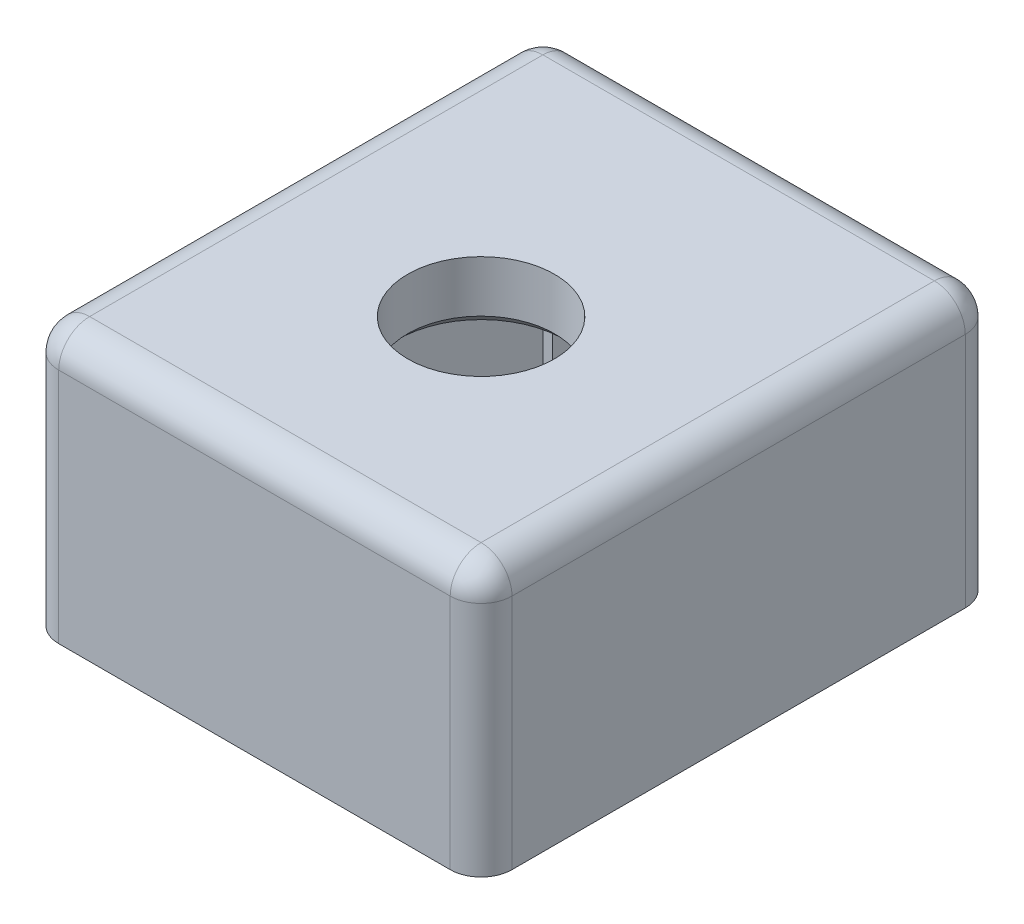
SolidWorks part; units mm, degrees
ref_plane "Front Plane" through (0, 0, 0) normal (0, 0, 1) x (1, 0, 0)
ref_plane "Top Plane" through (0, 0, 0) normal (0, 1, 0) x (1, 0, 0)
ref_plane "Right Plane" through (0, 0, 0) normal (1, 0, 0) x (0, 0, -1)
sketch "Sketch1" plane through (0, 0, 0) normal (0, 1, 0) x (1, 0, 0)
  line L0 (0, 0) -> (8.5, 0) construction
  line L1 (0, 0) -> (-11, 0) construction
  line L2 (8.5, -1.375) -> (6.5, -1.375) construction
  line L3 (8.5, -1.375) -> (8.5, 1.375) construction
  line L4 (8.5, 1.375) -> (6.5, 1.375) construction
  line L5 (6.5, -1.375) -> (6.5, 1.375) construction
  line L6 (8.5, -1.375) -> (6.5, 1.375) construction
  line L7 (8.5, 1.375) -> (6.5, -1.375) construction
  line L8 (11, -11) -> (-11, -11)
  line L9 (11, -11) -> (11, 14)
  line L10 (11, 14) -> (-11, 14)
  line L11 (-11, -11) -> (-11, 14)
  line L12 (11, -11) -> (-11, 14) construction
  line L13 (11, 14) -> (-11, -11) construction
  line L14 (0, 0) -> (0, -11) construction
  line L15 (0, 0) -> (0, 14) construction
  circle A0 centre (0, 0) radius 8.5 construction
  circle A1 centre (0, 0) radius 3.5625
  point P2 (0, 1.5)
  point P6 (7.5, 0)
  point P13 (8.5, 0)
  dimension "D1" = 17
  dimension "D2" = 7.125
  dimension "D3" = 2.75
  dimension "D4" = 2
  dimension "D5" = 25
  dimension "D6" = 22
extrude "Boss-Extrude1" add sketch "Sketch1" along normal blind 3
sketch3d "3DSketch1"
  line L0 (0, 0, 0) -> (8.5, 0, 0) construction
  line L1 (8.5, 0, -1.375) -> (6.5, 0, -1.375)
  line L2 (8.5, 0, -1.375) -> (8.5, 0, 1.375)
  line L3 (8.5, 0, 1.375) -> (6.5, 0, 1.375)
  line L4 (6.5, 0, -1.375) -> (6.5, 0, 1.375)
  line L5 (8.5, 0, -1.375) -> (6.5, 0, 1.375) construction
  line L6 (8.5, 0, 1.375) -> (6.5, 0, -1.375) construction
  point P0 (7.5, 0, 0)
  dimension "D1" = 8.5
  dimension "D2" = 2
  dimension "D3" = 2.75
extrude "Cut-Extrude1" cut sketch "3DSketch1" along direction (0, -1, 0) on the side against the normal blind 2
sketch "Sketch2" plane through (0, 0, 0) normal (0, -1, 0) x (1, 0, 0)
  line L0 (-11, 11) -> (11, 11) construction
  line L1 (11, -14) -> (-11, -14)
  line L2 (11, -14) -> (11, 11)
  line L3 (11, 11) -> (-11, 11)
  line L4 (-11, -14) -> (-11, 11)
  line L5 (11, -14) -> (-11, 11) construction
  line L6 (11, 11) -> (-11, -14) construction
  line L7 (-11, -14) -> (-11, 11) construction
  line L8 (9, 9) -> (-9, 9)
  line L9 (-9, -12) -> (-9, 9)
  line L10 (9, -12) -> (-9, -12)
  line L11 (9, -12) -> (9, 9)
  point P0 (0, -1.5)
  dimension "D1" = 2
extrude "Boss-Extrude2" add sketch "Sketch2" along normal blind 10
fillet "Fillet1" radius 1.5 8 edges at (0, 3, -14) (11, 3, -1.5) (11, -3.5, 11) (-11, 3, -1.5) (-11, -3.5, 11) (0, 3, 11) (-11, -3.5, -14) (11, -3.5, -14)
sketch "Sketch6" plane through (0, 0, -14) normal (0, 0, -1) x (-1, 0, 0)
  line L0 (0, -10) -> (0, 1.5) construction
  line L1 (9.5, -10) -> (-9.5, -10) construction
  line L2 (9.5, 1.5) -> (-9.5, 1.5) construction
  line L4 (8.5284, -18.5284) -> (-8.5284, -18.5284)
  line L5 (8.5284, -18.5284) -> (8.5284, -1.4716)
  line L6 (8.5284, -1.4716) -> (-8.5284, -1.4716)
  line L7 (-8.5284, -18.5284) -> (-8.5284, -1.4716)
  line L8 (8.5284, -18.5284) -> (-8.5284, -1.4716) construction
  line L9 (8.5284, -1.4716) -> (-8.5284, -18.5284) construction
chamfer "Chamfer2" distance 0.5 angle 45 1 edges at (0, 0, 3.5625)
fillet "Fillet2" radius 0.5 4 edges
extrude "Cut-Extrude4" cut sketch "Sketch6" against normal blind 3
